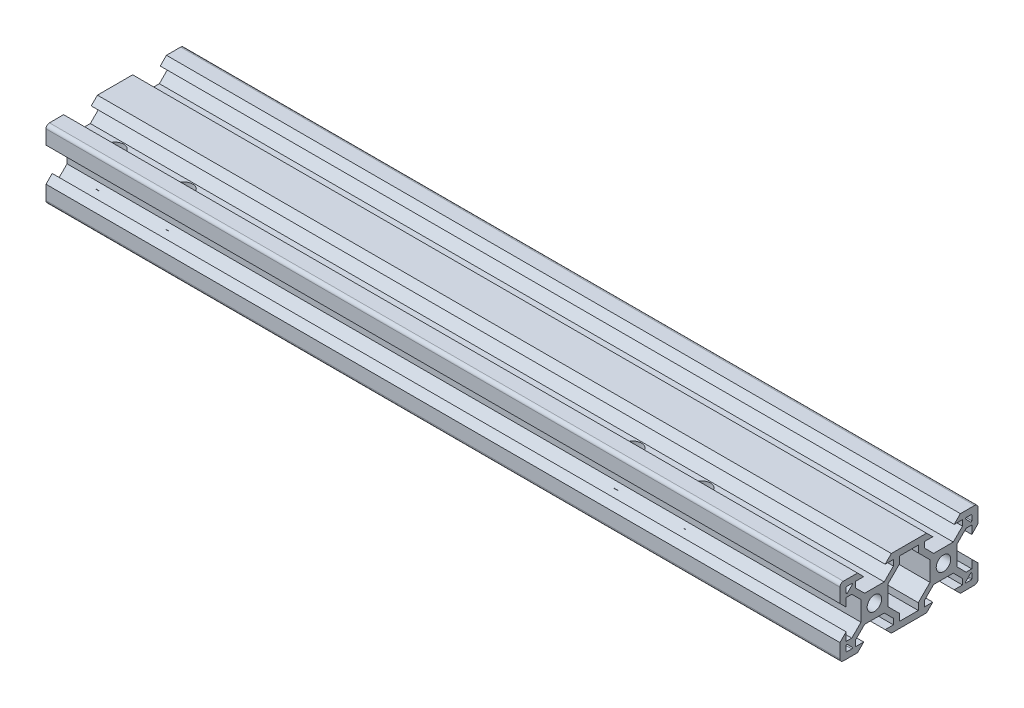
SolidWorks part; units mm, degrees
material "1060 Alloy"
ref_plane "Front Plane" through (0, 0, 0) normal (0, 0, 1) x (1, 0, 0)
ref_plane "Top Plane" through (0, 0, 0) normal (0, 1, 0) x (1, 0, 0)
ref_plane "Right Plane" through (0, 0, 0) normal (1, 0, 0) x (0, 0, -1)
sketch "Sketch4" plane through (0, 0, 0) normal (1, 0, 0) x (0, 0, -1)
  line L0 (-19.2399, 7.0114) -> (20.7601, 7.0114) construction
  dimension "D1" = 40
sketch "Sketch5" plane through (0, 0, 0) normal (1, 0, 0) x (0, 0, -1)
  line L0 (-19.998, 4.9) -> (-18.198, 3.1)
  line L1 (-18.198, 3.1) -> (-18.198, 5.4993)
  line L2 (-18.198, 5.4993) -> (-16.558, 5.4993)
  line L3 (-16.558, 5.4993) -> (-13.9, 2.8413)
  line L4 (-13.9, 2.8413) -> (-13.9, -2.8387)
  line L5 (-13.9, -2.8387) -> (-16.558, -5.4967)
  line L6 (-16.558, -5.4967) -> (-18.198, -5.4967)
  line L7 (-18.198, -5.4967) -> (-18.198, -3.1)
  line L8 (-18.198, -3.1) -> (-19.998, -4.9)
  line L9 (-19.998, -4.9) -> (-19.998, -9)
  line L10 (-18.998, -10) -> (-14.9, -10)
  line L11 (-14.9, -10) -> (-13.1, -8.2)
  line L12 (-13.1, -8.2) -> (-15.5, -8.2)
  line L13 (-15.5, -8.2) -> (-15.5, -6.56)
  line L14 (-15.5, -6.56) -> (-12.84, -3.9)
  line L15 (-12.84, -3.9) -> (-7.16, -3.9)
  line L16 (-7.16, -3.9) -> (-4.5, -6.56)
  line L17 (-4.5, -6.56) -> (-4.5, -8.2)
  line L18 (-4.5, -8.2) -> (-6.9, -8.2)
  line L19 (-6.9, -8.2) -> (-5.1, -10)
  line L20 (-5.1, -10) -> (5.1, -10)
  line L21 (5.1, -10) -> (6.9, -8.2)
  line L22 (6.9, -8.2) -> (4.496, -8.2)
  line L23 (4.496, -8.2) -> (4.496, -6.56)
  line L24 (4.496, -6.56) -> (7.156, -3.9)
  line L25 (7.156, -3.9) -> (12.836, -3.9)
  line L26 (12.836, -3.9) -> (15.496, -6.56)
  line L27 (15.496, -6.56) -> (15.496, -8.2)
  line L28 (15.496, -8.2) -> (13.1, -8.2)
  line L29 (13.1, -8.2) -> (14.9, -10)
  line L30 (14.9, -10) -> (19.002, -10)
  line L31 (20.002, -9) -> (20.002, -4.9)
  line L32 (20.002, -4.9) -> (18.202, -3.1)
  line L33 (18.202, -3.1) -> (18.202, -5.5046)
  line L34 (18.202, -5.5046) -> (16.562, -5.5046)
  line L35 (16.562, -5.5046) -> (13.9, -2.8426)
  line L36 (13.9, -2.8426) -> (13.9, 2.8374)
  line L37 (13.9, 2.8374) -> (16.562, 5.4993)
  line L38 (16.562, 5.4993) -> (18.202, 5.4993)
  line L39 (18.202, 5.4993) -> (18.202, 3.1)
  line L40 (18.202, 3.1) -> (20.002, 4.9)
  line L41 (20.002, 4.9) -> (20.002, 9)
  line L42 (19.002, 10) -> (14.9, 10)
  line L43 (14.9, 10) -> (13.1, 8.2)
  line L44 (13.1, 8.2) -> (15.5013, 8.2)
  line L45 (15.5013, 8.2) -> (15.5013, 6.56)
  line L46 (15.5013, 6.56) -> (12.8413, 3.9)
  line L47 (12.8413, 3.9) -> (7.1613, 3.9)
  line L48 (7.1613, 3.9) -> (4.5013, 6.56)
  line L49 (4.5013, 6.56) -> (4.5013, 8.2)
  line L50 (4.5013, 8.2) -> (6.9, 8.2)
  line L51 (6.9, 8.2) -> (5.1, 10)
  line L52 (5.1, 10) -> (-5.1, 10)
  line L53 (-5.1, 10) -> (-6.9, 8.2)
  line L54 (-6.9, 8.2) -> (-4.5013, 8.2)
  line L55 (-4.5013, 8.2) -> (-4.5013, 6.56)
  line L56 (-4.5013, 6.56) -> (-7.1613, 3.9)
  line L57 (-7.1613, 3.9) -> (-12.8413, 3.9)
  line L58 (-12.8413, 3.9) -> (-15.5013, 6.56)
  line L59 (-15.5013, 6.56) -> (-15.5013, 8.2)
  line L60 (-15.5013, 8.2) -> (-13.1, 8.2)
  line L61 (-13.1, 8.2) -> (-14.9, 10)
  line L62 (-14.9, 10) -> (-18.998, 10)
  line L63 (-19.998, 9) -> (-19.998, 4.9)
  line L64 (6.1, -2.84) -> (6.1, 2.84)
  line L65 (6.1, 2.84) -> (2.7, 6.24)
  line L66 (2.7, 6.24) -> (2.7, 8.2)
  line L67 (2.7, 8.2) -> (-2.7, 8.2)
  line L68 (-2.7, 8.2) -> (-2.7, 6.24)
  line L69 (-2.7, 6.24) -> (-6.1, 2.84)
  line L70 (-6.1, 2.84) -> (-6.1, -2.84)
  line L71 (-6.1, -2.84) -> (-2.7, -6.24)
  line L72 (-2.7, -6.24) -> (-2.7, -8.2)
  line L73 (-2.7, -8.2) -> (2.7, -8.2)
  line L74 (2.7, -8.2) -> (2.7, -6.24)
  line L75 (2.7, -6.24) -> (6.1, -2.84)
  line L76 (0, -8.2) -> (0, 8.2) construction
  line L77 (6.1, 0) -> (-6.1, 0) construction
  line L78 (16.562, 5.4993) -> (15.5013, 6.56) construction
  line L79 (16.5713, 8.2) -> (18.002, 8.2)
  line L81 (17.8606, 6.4279) -> (16.4299, 7.8586)
  line L82 (18.202, 8) -> (18.202, 6.5693)
  line L83 (18.002, 6.5693) -> (18.002, 8) construction
  line L84 (18.002, 8) -> (16.5713, 8) construction
  line L85 (16.5713, 8) -> (18.002, 6.5693) construction
  line L86 (16.5713, -8.2) -> (18.002, -8.2)
  line L87 (18.202, -8) -> (18.202, -6.5693)
  line L88 (17.8606, -6.4279) -> (16.4299, -7.8586)
  line L89 (-17.8606, 6.4279) -> (-16.4299, 7.8586)
  line L90 (-16.5713, 8.2) -> (-18.002, 8.2)
  line L91 (-18.202, 8) -> (-18.202, 6.5693)
  line L92 (-16.5713, -8.2) -> (-18.002, -8.2)
  line L93 (-17.8606, -6.4279) -> (-16.4299, -7.8586)
  line L94 (-18.202, -8) -> (-18.202, -6.5693)
  circle A0 centre (-10, 0) radius 2.1
  circle A1 centre (10, 0) radius 2.1
  arc A2 (-19.998, -9) -> (-18.998, -10) centre (-18.998, -9) ccw
  arc A5 (-18.998, 10) -> (-19.998, 9) centre (-18.998, 9) ccw
  arc A6 (20.002, -9) -> (19.002, -10) centre (19.002, -9) cw
  arc A7 (20.002, 9) -> (19.002, 10) centre (19.002, 9) ccw
  arc A8 (18.002, 8.2) -> (18.202, 8) centre (18.002, 8) cw
  arc A10 (16.4299, 7.8586) -> (16.5713, 8.2) centre (16.5713, 8) cw
  arc A12 (18.202, 6.5693) -> (17.8606, 6.4279) centre (18.002, 6.5693) cw
  arc A13 (16.4299, -7.8586) -> (16.5713, -8.2) centre (16.5713, -8) ccw
  arc A14 (18.002, -8.2) -> (18.202, -8) centre (18.002, -8) ccw
  arc A15 (18.202, -6.5693) -> (17.8606, -6.4279) centre (18.002, -6.5693) ccw
  arc A16 (-18.202, 6.5693) -> (-17.8606, 6.4279) centre (-18.002, 6.5693) ccw
  arc A17 (-16.4299, 7.8586) -> (-16.5713, 8.2) centre (-16.5713, 8) ccw
  arc A18 (-18.002, 8.2) -> (-18.202, 8) centre (-18.002, 8) ccw
  arc A19 (-18.002, -8.2) -> (-18.202, -8) centre (-18.002, -8) cw
  arc A20 (-16.4299, -7.8586) -> (-16.5713, -8.2) centre (-16.5713, -8) cw
  arc A21 (-18.202, -6.5693) -> (-17.8606, -6.4279) centre (-18.002, -6.5693) cw
  dimension "D1" = 4.2
  dimension "D20" = 3.9
  dimension "D27" = 1
  dimension "D40" = 1
  dimension "D41" = 1
  dimension "D42" = 1
  dimension "D45" = 0.2
  dimension "D47" = 1.07
  dimension "D48" = 1.07
  dimension "D49" = 0.2
  dimension "D2" = 20
  dimension "D3" = 10
  dimension "D4" = 5.68
  dimension "D5" = 5.4
  dimension "D6" = 1.96
  dimension "D7" = 45
  dimension "D8" = 1.8
  dimension "D9" = 1.64
  dimension "D10" = 1.8
  dimension "D11" = 40
  dimension "D12" = 20
  dimension "D13" = 3.9
  dimension "D14" = 1.5
  dimension "D15" = 1.5
  dimension "D16" = 3.9
  dimension "D17" = 3.9
  dimension "D18" = 3.9
  dimension "D19" = 3.9
  dimension "D21" = 1.5
  dimension "D22" = 1.5
  dimension "D23" = 1.64
  dimension "D24" = 45
  dimension "D25" = 1.5
  dimension "D26" = 1.8
  dimension "D28" = 6.2
  dimension "D29" = 6.2
  dimension "D30" = 6.2
  dimension "D31" = 6.2
  dimension "D32" = 6.2
  dimension "D33" = 3.1
  dimension "D34" = 3.1
  dimension "D35" = 3.1
  dimension "D36" = 3.1
  dimension "D37" = 6.2
  dimension "D38" = 3.1
  dimension "D39" = 3.1
  dimension "D43" = 1.64
  dimension "D44" = 135
  dimension "D46" = 45
extrude "Boss-Extrude1" add sketch "Sketch5" along normal mid plane 230
sketch "Sketch7" plane through (0, -10, 0) normal (0, -1, 0) x (1, 0, 0)
  line L0 (115, 10) -> (-115, 10) construction
  line L1 (115, 12.84) -> (115, 7.16) construction
  line L2 (-115, 12.84) -> (-115, 7.16) construction
  circle A0 centre (-105, 10) radius 2.5
  circle A1 centre (-85, 10) radius 2.5
  circle A2 centre (65, 10) radius 2.5
  circle A3 centre (45, 10) radius 2.5
  dimension "D1" = 5
  dimension "D2" = 10
  dimension "D4" = 20
  dimension "D6" = 150
  dimension "D3" = 2
  dimension "D5" = 2
extrude "Cut-Extrude1" cut sketch "Sketch7" against normal up to next
sketch "Sketch8" plane through (0, -10, 0) normal (0, -1, 0) x (1, 0, 0)
  circle A0 centre (-105, 10) radius 5
  circle A1 centre (-85, 10) radius 5
  circle A2 centre (45, 10) radius 5
  circle A3 centre (65, 10) radius 5
  dimension "D1" = 10
  dimension "D3" = 20
  dimension "D5" = 150
  dimension "D2" = 2
  dimension "D4" = 2
extrude "Cut-Extrude2" cut sketch "Sketch8" against normal up to surface (6.1 mm away) up to face at (-105, -3.9, 12.5)
